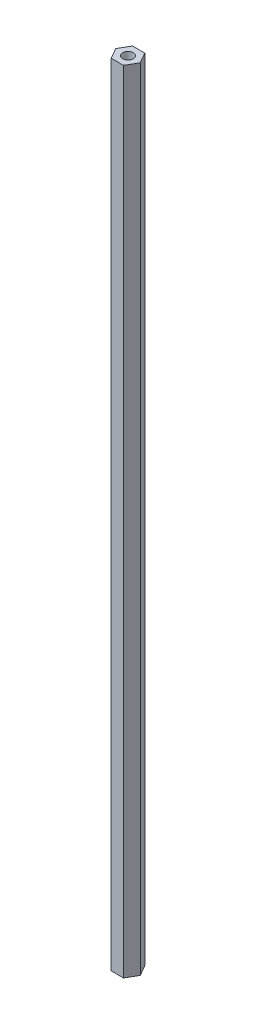
SolidWorks part; units mm, degrees
material "6061-T6 (SS)"
ref_plane "Front Plane" through (0, 0, 0) normal (0, 0, 1) x (1, 0, 0)
ref_plane "Top Plane" through (0, 0, 0) normal (0, 1, 0) x (1, 0, 0)
ref_plane "Right Plane" through (0, 0, 0) normal (1, 0, 0) x (0, 0, -1)
sketch "Sketch1" plane through (0, 0, 0) normal (0, 1, 0) x (1, 0, 0)
  line L1 (3.6662, -6.35) -> (7.3323, 0)
  line L2 (7.3323, 0) -> (3.6662, 6.35)
  line L3 (3.6662, 6.35) -> (-3.6662, 6.35)
  line L4 (-3.6662, 6.35) -> (-7.3323, 0)
  line L5 (-7.3323, 0) -> (-3.6662, -6.35)
  line L6 (-3.6662, -6.35) -> (3.6662, -6.35)
  circle A0 centre (0, 0) radius 6.35 construction
  circle A1 centre (0, 0) radius 3.175
  dimension "D1" = 12.7
  dimension "D2" = 6.35
extrude "Boss-Extrude1" add sketch "Sketch1" along normal blind 472.44
